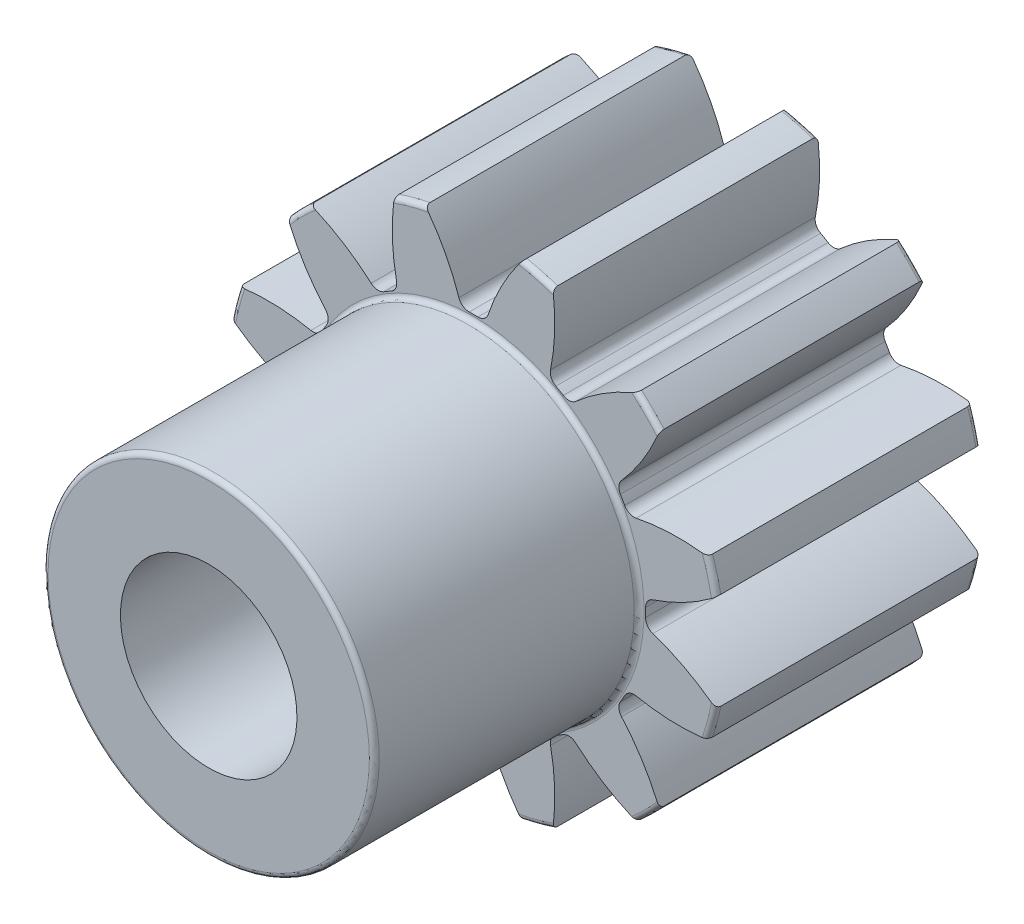
SolidWorks part; units mm, degrees
ref_plane "Front Plane" through (0, 0, 0) normal (0, 0, 1) x (1, 0, 0)
ref_plane "Top Plane" through (0, 0, 0) normal (0, 1, 0) x (1, 0, 0)
ref_plane "Right Plane" through (0, 0, 0) normal (1, 0, 0) x (0, 0, -1)
sketch "Sketch1" plane through (0, 0, 0) normal (0, 0, 1) x (1, 0, 0)
  line L0 (-152.4, 0) -> (152.4, 0) construction
  circle A0 centre (0, 0) radius 8.89 construction
  circle A1 centre (0, 0) radius 7.62 construction
  circle A2 centre (0, 0) radius 6.1912 construction
  circle A3 centre (0, 0) radius 5.9563 construction
  circle A4 centre (0, 0) radius 3.175 construction
  dimension "D2" = 1.27
  dimension "D3" = 2.6987
  dimension "D1" = 2.6987
sketch "Sketch2" plane through (0, 0, 0) normal (1, 0, 0) x (0, 0, -1)
  line L0 (0, 0) -> (-9.525, 0) construction
  line L1 (-9.525, 0) -> (-19.05, 0) construction
  dimension "Overall Width" = 19.05
  dimension "Face Width" = 9.525
sketch "Sketch4" plane through (0, 0, 0) normal (1, 0, 0) x (0, 0, -1)
  line L0 (-19.05, 3.175) -> (-19.05, 5.9563)
  line L1 (-19.05, 5.9563) -> (-9.525, 5.9563)
  line L2 (-9.525, 5.9563) -> (-9.525, 8.89)
  line L3 (-9.525, 8.89) -> (0, 8.89)
  line L4 (0, 8.89) -> (0, 3.175)
  line L5 (-9.525, 5.9563) -> (-9.525, 0) construction
  line L6 (0, 8.89) -> (0, -8.89) construction
  line L7 (-9.525, 5.9563) -> (0, 5.9563) construction
  line L12 (-19.05, 3.175) -> (0, 3.175)
revolve "Revolve1" add sketch "Sketch4" angle 360 about L1
fillet "Fillet2" radius 0.1778 4 edges at (0, 5.9563, 19.05) (0, 5.9563, 9.525) (0, 8.89, 9.525) (0, 8.89, 0)
sketch "Sketch7" plane through (0, 0, 9.525) normal (0, 0, 1) x (1, 0, 0)
  line L0 (0, 0) -> (0, 8.89) construction
  line L1 (0.9946, 7.5548) -> (1.6129, 8.7425) construction
  line L3 (2.3009, 8.5871) -> (1.9722, 7.3604) construction
  line L4 (1.9722, 7.3604) -> (1.6024, 5.9803) construction
  line L5 (0, 0) -> (1.6024, 5.9803) construction
  line L6 (0.9946, 7.5548) -> (0, 0) construction
  line L7 (0.9946, 7.5548) -> (1.1604, 8.8139) construction
  line L8 (0.9946, 7.5548) -> (0, 0) construction
  circle A0 centre (0, 0) radius 8.89 construction
  arc A1 (-0.1549, 6.1893) -> (0.1549, 6.1893) centre (0, 0) cw
  circle A2 centre (0, 0) radius 6.1912 construction
  arc A3 (-0.9946, 7.5548) -> (0.9946, 7.5548) centre (0, 0) cw construction
  circle A4 centre (0, 0) radius 7.62 construction
  arc A5 (2.8509, 8.4205) -> (1.7413, 8.7178) centre (0, 0) ccw construction
  arc A6 (0.9946, 7.5548) -> (2.916, 7.04) centre (0, 0) cw construction
  arc A7 (-1.7413, 8.7178) -> (1.7413, 8.7178) centre (0, 0) cw
  arc A8 (0.5259, 6.4495) -> (1.7413, 8.7178) centre (7.7536, 4.0363) cw
  arc A9 (-0.5259, 6.4495) -> (-1.7413, 8.7178) centre (-7.7536, 4.0363) ccw
  arc A10 (-0.1549, 6.1893) -> (-0.5259, 6.4495) centre (-0.1645, 6.5702) cw
  arc A11 (0.1549, 6.1893) -> (0.5259, 6.4495) centre (0.1645, 6.5702) ccw
  point P26 (-0.4401, 6.1756)
  point P29 (0.4401, 6.1756)
  dimension "D4" = 0.381
  dimension "D5" = 7.62
  dimension "D3" = 20
  dimension "D1" = 3.9898
  dimension "D2" = 1.9949
extrude "Cut-Extrude2" cut sketch "Sketch7" against normal through all
pattern_circular "CirPattern1" count 12 over 360 about axis through (0, 0, 0) along (0, 0, 1) of "Cut-Extrude2"
equation "\"D1@Sketch1\"=2.125*(\"Pitch Dia.@Sketch1\"/\"Number of Teeth@Sketch1\")"
equation "\"D1@CirPattern1\"=\"Number of Teeth@Sketch1\""
equation "\"D1@Fillet2\"=\"OD@Sketch1\"*.01"
equation "\"D1@Sketch7\"=3.14159*(\"Pitch Dia.@Sketch1\"/\"Number of Teeth@Sketch1\")"
equation "\"D2@Sketch7\"=\"D1@Sketch7\"/2"
equation "\"D4@Sketch7\"=\"D1@Sketch7\"*.0955"
equation "\"D5@Sketch7\"=\"Pitch Dia.@Sketch1\"/2"
